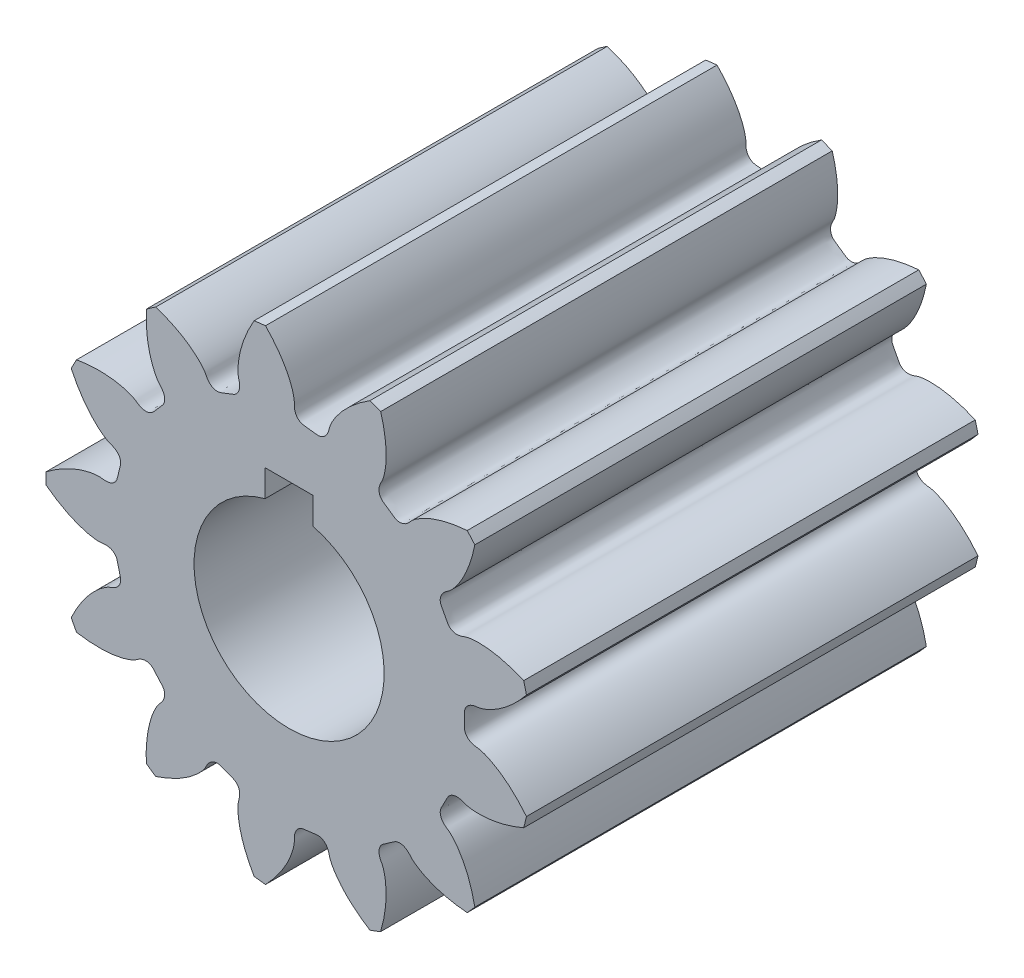
SolidWorks part; units mm, degrees
material "AISI 4130 Steel, annealed at 865C"
ref_plane "Front Plane" through (0, 0, 0) normal (0, 0, 1) x (1, 0, 0)
ref_plane "Top Plane" through (0, 0, 0) normal (0, 1, 0) x (1, 0, 0)
ref_plane "Right Plane" through (0, 0, 0) normal (1, 0, 0) x (0, 0, -1)
ref_plane "Plane1" through (0, 0, 9.5) normal (0, 0, 1) x (1, 0, 0)
sketch "Sketch1" plane through (0, 0, 9.5) normal (0, 0, 1) x (1, 0, 0)
  line L0 (1.01, 5) -> (1.01, 3.8704)
  line L1 (-1.01, 3.8704) -> (-1.01, 5)
  line L2 (-1.01, 5) -> (1.01, 5)
  arc A0 (1.01, 3.8704) -> (-1.01, 3.8704) centre (0, 0) cw
  arc A1 (7.8147, 6.6005) -> (7.4944, 6.9621) centre (0, 0) ccw
  arc A2 (3.8522, 9.4762) -> (3.4005, 9.6475) centre (0, 0) ccw
  arc A3 (-0.9929, 10.1809) -> (-1.4725, 10.1227) centre (0, 0) ccw
  arc A4 (-5.6104, 8.5534) -> (-6.008, 8.2789) centre (0, 0) ccw
  arc A5 (-8.9427, 4.9663) -> (-9.1673, 4.5385) centre (0, 0) ccw
  arc A6 (-10.2264, 0.2416) -> (-10.2264, -0.2416) centre (0, 0) ccw
  arc A7 (-9.1673, -4.5385) -> (-8.9427, -4.9663) centre (0, 0) ccw
  arc A8 (-6.008, -8.2789) -> (-5.6104, -8.5534) centre (0, 0) ccw
  arc A9 (-1.4725, -10.1227) -> (-0.9929, -10.1809) centre (0, 0) ccw
  arc A10 (3.4005, -9.6475) -> (3.8522, -9.4762) centre (0, 0) ccw
  arc A11 (7.4944, -6.9621) -> (7.8147, -6.6005) centre (0, 0) ccw
  arc A12 (9.8714, -2.6819) -> (9.987, -2.2128) centre (0, 0) ccw
  arc A13 (9.987, 2.2128) -> (9.8714, 2.6819) centre (0, 0) ccw
  spline S0 degree 3 poles (3.8522, 9.4762) (3.9191, 9.2499) (3.99, 8.9516) (4.0451, 8.5838) (4.0666, 8.3872) (4.0793, 8.2028) (4.0843, 8.0307) (4.0826, 7.8712) (4.0751, 7.7248) (4.063, 7.5914) (4.0473, 7.4713) (4.0289, 7.3644) (4.009, 7.2709) (3.9885, 7.1905) (3.9684, 7.1233) (3.9499, 7.069) (3.9338, 7.0274) (3.9101, 6.9717) (3.8779, 6.9207) (3.8503, 6.8634) (3.8331, 6.8241) (3.818, 6.7841) (3.805, 6.7428) (3.7942, 6.6993) (3.7861, 6.652) (3.7819, 6.5989) (3.7839, 6.5372) (3.7968, 6.4642) (3.8286, 6.3799) (3.8867, 6.2926) (4.0132, 6.1898) (4.199, 6.0833) (4.3645, 5.9473) (4.5054, 5.8655) (4.6076, 5.8421) (4.6978, 5.8423) (4.7706, 5.8562) (4.829, 5.8761) (4.8771, 5.8989) (4.9185, 5.9232) (4.9554, 5.9487) (4.9894, 5.9756) (5.0214, 6.0039) (5.052, 6.0339) (5.0959, 6.0801) (5.1321, 6.1282) (5.1758, 6.1701) (5.209, 6.1999) (5.2532, 6.2365) (5.3089, 6.2791) (5.3768, 6.3267) (5.4572, 6.3785) (5.5506, 6.4336) (5.6573, 6.4909) (5.7777, 6.5496) (5.912, 6.6084) (6.0605, 6.6666) (6.2232, 6.7229) (6.4002, 6.7765) (6.5916, 6.8261) (6.955, 6.905) (7.2591, 6.9445) (7.4944, 6.9621) knots 0 0 0 0 0.096899 0.125711 0.152776 0.178096 0.201669 0.223496 0.243577 0.261912 0.2785 0.293343 0.306439 0.317789 0.327393 0.335251 0.341362 0.345728 0.360077 0.366027 0.371876 0.377693 0.383571 0.389648 0.396117 0.403265 0.411505 0.421399 0.433571 0.448325 0.46384 0.5 0.53616 0.551675 0.566429 0.578601 0.588495 0.596735 0.603883 0.610352 0.616429 0.622307 0.628124 0.633973 0.639923 0.654272 0.658638 0.664749 0.672607 0.682211 0.693561 0.706657 0.7215 0.738088 0.756423 0.776504 0.798331 0.821904 0.847224 0.874289 0.903101 1 1 1 1
  spline S1 degree 3 poles (-0.9929, 10.1809) (-0.8284, 10.0117) (-0.6271, 9.7805) (-0.4073, 9.4804) (-0.297, 9.3164) (-0.2, 9.1589) (-0.1156, 9.0089) (-0.043, 8.8669) (0.0185, 8.7337) (0.0697, 8.61) (0.1116, 8.4963) (0.145, 8.3932) (0.1708, 8.3011) (0.19, 8.2204) (0.2035, 8.1516) (0.2124, 8.0949) (0.2174, 8.0506) (0.2223, 7.9903) (0.2175, 7.9302) (0.2197, 7.8665) (0.2228, 7.8238) (0.228, 7.7813) (0.2356, 7.7387) (0.2462, 7.6951) (0.2611, 7.6495) (0.2821, 7.6005) (0.3125, 7.5469) (0.3578, 7.4883) (0.4252, 7.4283) (0.5172, 7.3781) (0.6769, 7.3459) (0.891, 7.3379) (1.1007, 7.2944) (1.2635, 7.2875) (1.3649, 7.3142) (1.4446, 7.3563) (1.5027, 7.4024) (1.5451, 7.4472) (1.5771, 7.4897) (1.6025, 7.5305) (1.6233, 7.5702) (1.6409, 7.6098) (1.6561, 7.6497) (1.6693, 7.6905) (1.6866, 7.7518) (1.6963, 7.8113) (1.7155, 7.8686) (1.731, 7.9105) (1.7532, 7.9634) (1.7828, 8.027) (1.8207, 8.1007) (1.8678, 8.184) (1.9249, 8.2761) (1.9928, 8.3765) (2.0722, 8.4844) (2.1638, 8.5989) (2.2682, 8.7194) (2.386, 8.8449) (2.5179, 8.9746) (2.6643, 9.1074) (2.9495, 9.3462) (3.2003, 9.5225) (3.4005, 9.6475) knots 0 0 0 0 0.096899 0.125711 0.152776 0.178096 0.201669 0.223496 0.243577 0.261912 0.2785 0.293343 0.306439 0.317789 0.327393 0.335251 0.341362 0.345728 0.360077 0.366027 0.371876 0.377693 0.383571 0.389648 0.396117 0.403265 0.411505 0.421399 0.433571 0.448325 0.46384 0.5 0.53616 0.551675 0.566429 0.578601 0.588495 0.596735 0.603883 0.610352 0.616429 0.622307 0.628124 0.633973 0.639923 0.654272 0.658638 0.664749 0.672607 0.682211 0.693561 0.706657 0.7215 0.738088 0.756423 0.776504 0.798331 0.821904 0.847224 0.874289 0.903101 1 1 1 1
  spline S2 degree 3 poles (-5.6104, 8.5534) (-5.3862, 8.4799) (-5.1005, 8.3688) (-4.7664, 8.2052) (-4.5925, 8.1112) (-4.4334, 8.0169) (-4.289, 7.9232) (-4.1587, 7.8313) (-4.0424, 7.7419) (-3.9395, 7.6562) (-3.8496, 7.575) (-3.7721, 7.4992) (-3.7065, 7.4296) (-3.652, 7.3671) (-3.608, 7.3125) (-3.5738, 7.2664) (-3.5488, 7.2294) (-3.5164, 7.1784) (-3.4927, 7.1229) (-3.4612, 7.0676) (-3.4386, 7.0311) (-3.4143, 6.996) (-3.3878, 6.9618) (-3.3581, 6.9282) (-3.3237, 6.8947) (-3.2824, 6.861) (-3.2305, 6.8277) (-3.1631, 6.7968) (-3.0756, 6.775) (-2.9708, 6.7733) (-2.8144, 6.819) (-2.6212, 6.9114) (-2.4153, 6.9704) (-2.2679, 7.0399) (-2.1905, 7.1107) (-2.1395, 7.185) (-2.1095, 7.2528) (-2.0928, 7.3122) (-2.0842, 7.3648) (-2.0807, 7.4126) (-2.0807, 7.4575) (-2.0835, 7.5007) (-2.0886, 7.5431) (-2.0959, 7.5854) (-2.109, 7.6477) (-2.1281, 7.7049) (-2.1377, 7.7646) (-2.1434, 7.8088) (-2.1484, 7.866) (-2.1518, 7.9361) (-2.1524, 8.019) (-2.1494, 8.1146) (-2.1417, 8.2227) (-2.1282, 8.3431) (-2.1081, 8.4755) (-2.0802, 8.6195) (-2.0438, 8.7747) (-1.9977, 8.9406) (-1.9412, 9.1167) (-1.8733, 9.3024) (-1.7318, 9.6464) (-1.5916, 9.9191) (-1.4725, 10.1227) knots 0 0 0 0 0.096899 0.125711 0.152776 0.178096 0.201669 0.223496 0.243577 0.261912 0.2785 0.293343 0.306439 0.317789 0.327393 0.335251 0.341362 0.345728 0.360077 0.366027 0.371876 0.377693 0.383571 0.389648 0.396117 0.403265 0.411505 0.421399 0.433571 0.448325 0.46384 0.5 0.53616 0.551675 0.566429 0.578601 0.588495 0.596735 0.603883 0.610352 0.616429 0.622307 0.628124 0.633973 0.639923 0.654272 0.658638 0.664749 0.672607 0.682211 0.693561 0.706657 0.7215 0.738088 0.756423 0.776504 0.798331 0.821904 0.847224 0.874289 0.903101 1 1 1 1
  spline S3 degree 3 poles (-8.9427, 4.9663) (-8.7101, 5.0055) (-8.4054, 5.0399) (-8.0336, 5.0502) (-7.8359, 5.0479) (-7.6512, 5.0383) (-7.4798, 5.0225) (-7.3217, 5.0016) (-7.1772, 4.9765) (-7.0463, 4.9484) (-6.9289, 4.9183) (-6.8251, 4.8872) (-6.7346, 4.8561) (-6.6574, 4.8261) (-6.593, 4.7981) (-6.5413, 4.7732) (-6.502, 4.7522) (-6.4496, 4.722) (-6.4028, 4.6839) (-6.3492, 4.6495) (-6.3123, 4.6277) (-6.2744, 4.6079) (-6.235, 4.59) (-6.1931, 4.574) (-6.1471, 4.5603) (-6.0949, 4.5497) (-6.0334, 4.5443) (-5.9594, 4.5483) (-5.8718, 4.5697) (-5.7782, 4.6169) (-5.661, 4.73) (-5.5328, 4.9017) (-5.3779, 5.0495) (-5.2797, 5.1796) (-5.2441, 5.2782) (-5.2335, 5.3678) (-5.2384, 5.4417) (-5.2512, 5.502) (-5.268, 5.5526) (-5.2871, 5.5966) (-5.3081, 5.6363) (-5.3306, 5.6733) (-5.3548, 5.7085) (-5.3809, 5.7425) (-5.4215, 5.7916) (-5.465, 5.8334) (-5.5012, 5.8818) (-5.5269, 5.9183) (-5.5578, 5.9666) (-5.5934, 6.0271) (-5.6325, 6.1002) (-5.6742, 6.1862) (-5.7176, 6.2856) (-5.7617, 6.3985) (-5.8054, 6.525) (-5.8476, 6.6655) (-5.8875, 6.8199) (-5.9238, 6.9882) (-5.9556, 7.1703) (-5.9818, 7.3663) (-6.0163, 7.7366) (-6.0189, 8.0432) (-6.008, 8.2789) knots 0 0 0 0 0.096899 0.125711 0.152776 0.178096 0.201669 0.223496 0.243577 0.261912 0.2785 0.293343 0.306439 0.317789 0.327393 0.335251 0.341362 0.345728 0.360077 0.366027 0.371876 0.377693 0.383571 0.389648 0.396117 0.403265 0.411505 0.421399 0.433571 0.448325 0.46384 0.5 0.53616 0.551675 0.566429 0.578601 0.588495 0.596735 0.603883 0.610352 0.616429 0.622307 0.628124 0.633973 0.639923 0.654272 0.658638 0.664749 0.672607 0.682211 0.693561 0.706657 0.7215 0.738088 0.756423 0.776504 0.798331 0.821904 0.847224 0.874289 0.903101 1 1 1 1
  spline S4 degree 3 poles (-10.2264, 0.2416) (-10.0386, 0.3844) (-9.7848, 0.5564) (-9.4604, 0.7384) (-9.2842, 0.8281) (-9.1162, 0.9055) (-8.9571, 0.9712) (-8.8074, 1.0261) (-8.6678, 1.0711) (-8.5388, 1.107) (-8.4209, 1.1349) (-8.3145, 1.1556) (-8.22, 1.1702) (-8.1376, 1.1795) (-8.0676, 1.1846) (-8.0103, 1.1865) (-7.9656, 1.1862) (-7.9052, 1.1838) (-7.8461, 1.1718) (-7.7827, 1.1663) (-7.7399, 1.1642) (-7.6971, 1.1642) (-7.6539, 1.1666) (-7.6094, 1.172) (-7.5623, 1.1812) (-7.5111, 1.1962) (-7.4542, 1.2199) (-7.3905, 1.2578) (-7.3229, 1.3175) (-7.262, 1.4028) (-7.2107, 1.5575) (-7.177, 1.769) (-7.1085, 1.9719) (-7.082, 2.1327) (-7.0964, 2.2366) (-7.1285, 2.3208) (-7.1673, 2.384) (-7.2066, 2.4314) (-7.245, 2.4684) (-7.2824, 2.4985) (-7.3194, 2.5239) (-7.3565, 2.5462) (-7.3943, 2.5661) (-7.4332, 2.5841) (-7.492, 2.6087) (-7.5499, 2.6255) (-7.6045, 2.6515) (-7.6442, 2.6719) (-7.694, 2.7003) (-7.7536, 2.7373) (-7.8222, 2.7839) (-7.8992, 2.8407) (-7.9838, 2.9085) (-8.0752, 2.988) (-8.1727, 3.0797) (-8.2754, 3.1845) (-8.3824, 3.3026) (-8.4928, 3.4348) (-8.6056, 3.5813) (-8.7199, 3.7427) (-8.9225, 4.0546) (-9.0673, 4.3248) (-9.1673, 4.5385) knots 0 0 0 0 0.096899 0.125711 0.152776 0.178096 0.201669 0.223496 0.243577 0.261912 0.2785 0.293343 0.306439 0.317789 0.327393 0.335251 0.341362 0.345728 0.360077 0.366027 0.371876 0.377693 0.383571 0.389648 0.396117 0.403265 0.411505 0.421399 0.433571 0.448325 0.46384 0.5 0.53616 0.551675 0.566429 0.578601 0.588495 0.596735 0.603883 0.610352 0.616429 0.622307 0.628124 0.633973 0.639923 0.654272 0.658638 0.664749 0.672607 0.682211 0.693561 0.706657 0.7215 0.738088 0.756423 0.776504 0.798331 0.821904 0.847224 0.874289 0.903101 1 1 1 1
  spline S5 degree 3 poles (-9.1673, -4.5385) (-9.0673, -4.3248) (-8.9225, -4.0546) (-8.7199, -3.7427) (-8.6056, -3.5813) (-8.4928, -3.4348) (-8.3824, -3.3026) (-8.2754, -3.1845) (-8.1727, -3.0797) (-8.0752, -2.988) (-7.9838, -2.9085) (-7.8992, -2.8407) (-7.8222, -2.7839) (-7.7536, -2.7373) (-7.694, -2.7003) (-7.6442, -2.6719) (-7.6045, -2.6515) (-7.5499, -2.6255) (-7.492, -2.6087) (-7.4332, -2.5841) (-7.3943, -2.5661) (-7.3565, -2.5462) (-7.3194, -2.5239) (-7.2824, -2.4985) (-7.245, -2.4684) (-7.2066, -2.4314) (-7.1673, -2.384) (-7.1285, -2.3208) (-7.0964, -2.2366) (-7.082, -2.1327) (-7.1085, -1.9719) (-7.177, -1.769) (-7.2107, -1.5575) (-7.262, -1.4028) (-7.3229, -1.3175) (-7.3905, -1.2578) (-7.4542, -1.2199) (-7.5111, -1.1962) (-7.5623, -1.1812) (-7.6094, -1.172) (-7.6539, -1.1666) (-7.6971, -1.1642) (-7.7399, -1.1642) (-7.7827, -1.1663) (-7.8461, -1.1718) (-7.9052, -1.1838) (-7.9656, -1.1862) (-8.0103, -1.1865) (-8.0676, -1.1846) (-8.1376, -1.1795) (-8.22, -1.1702) (-8.3145, -1.1556) (-8.4209, -1.1349) (-8.5388, -1.107) (-8.6678, -1.0711) (-8.8074, -1.0261) (-8.9571, -0.9712) (-9.1162, -0.9055) (-9.2842, -0.8281) (-9.4604, -0.7384) (-9.7848, -0.5564) (-10.0386, -0.3844) (-10.2264, -0.2416) knots 0 0 0 0 0.096899 0.125711 0.152776 0.178096 0.201669 0.223496 0.243577 0.261912 0.2785 0.293343 0.306439 0.317789 0.327393 0.335251 0.341362 0.345728 0.360077 0.366027 0.371876 0.377693 0.383571 0.389648 0.396117 0.403265 0.411505 0.421399 0.433571 0.448325 0.46384 0.5 0.53616 0.551675 0.566429 0.578601 0.588495 0.596735 0.603883 0.610352 0.616429 0.622307 0.628124 0.633973 0.639923 0.654272 0.658638 0.664749 0.672607 0.682211 0.693561 0.706657 0.7215 0.738088 0.756423 0.776504 0.798331 0.821904 0.847224 0.874289 0.903101 1 1 1 1
  spline S6 degree 3 poles (-6.008, -8.2789) (-6.0189, -8.0432) (-6.0163, -7.7366) (-5.9818, -7.3663) (-5.9556, -7.1703) (-5.9238, -6.9882) (-5.8875, -6.8199) (-5.8476, -6.6655) (-5.8054, -6.525) (-5.7617, -6.3985) (-5.7176, -6.2856) (-5.6742, -6.1862) (-5.6325, -6.1002) (-5.5934, -6.0271) (-5.5578, -5.9666) (-5.5269, -5.9183) (-5.5012, -5.8818) (-5.465, -5.8334) (-5.4215, -5.7916) (-5.3809, -5.7425) (-5.3548, -5.7084) (-5.3306, -5.6733) (-5.3081, -5.6363) (-5.2871, -5.5966) (-5.268, -5.5526) (-5.2512, -5.502) (-5.2384, -5.4417) (-5.2335, -5.3678) (-5.2441, -5.2782) (-5.2797, -5.1796) (-5.3779, -5.0495) (-5.5328, -4.9017) (-5.661, -4.73) (-5.7782, -4.6169) (-5.8718, -4.5697) (-5.9594, -4.5483) (-6.0334, -4.5443) (-6.0949, -4.5497) (-6.1471, -4.5603) (-6.1931, -4.574) (-6.235, -4.59) (-6.2744, -4.6079) (-6.3123, -4.6277) (-6.3492, -4.6495) (-6.4028, -4.6839) (-6.4496, -4.722) (-6.502, -4.7522) (-6.5413, -4.7732) (-6.593, -4.7981) (-6.6574, -4.8261) (-6.7346, -4.8561) (-6.8251, -4.8872) (-6.9289, -4.9183) (-7.0463, -4.9484) (-7.1772, -4.9765) (-7.3217, -5.0016) (-7.4798, -5.0225) (-7.6512, -5.0383) (-7.8359, -5.0479) (-8.0336, -5.0502) (-8.4054, -5.0399) (-8.7101, -5.0055) (-8.9427, -4.9663) knots 0 0 0 0 0.096899 0.125711 0.152776 0.178096 0.201669 0.223496 0.243577 0.261912 0.2785 0.293343 0.306439 0.317789 0.327393 0.335251 0.341362 0.345728 0.360077 0.366027 0.371876 0.377693 0.383571 0.389648 0.396117 0.403265 0.411505 0.421399 0.433571 0.448325 0.46384 0.5 0.53616 0.551675 0.566429 0.578601 0.588495 0.596735 0.603883 0.610352 0.616429 0.622307 0.628124 0.633973 0.639923 0.654272 0.658638 0.664749 0.672607 0.682211 0.693561 0.706657 0.7215 0.738088 0.756423 0.776504 0.798331 0.821904 0.847224 0.874289 0.903101 1 1 1 1
  spline S7 degree 3 poles (-1.4725, -10.1227) (-1.5916, -9.9191) (-1.7318, -9.6464) (-1.8733, -9.3024) (-1.9412, -9.1167) (-1.9977, -8.9406) (-2.0438, -8.7747) (-2.0802, -8.6195) (-2.1081, -8.4755) (-2.1282, -8.3431) (-2.1417, -8.2227) (-2.1494, -8.1146) (-2.1524, -8.019) (-2.1518, -7.9361) (-2.1484, -7.866) (-2.1434, -7.8088) (-2.1377, -7.7646) (-2.1281, -7.7049) (-2.109, -7.6477) (-2.0959, -7.5854) (-2.0886, -7.5431) (-2.0835, -7.5007) (-2.0807, -7.4575) (-2.0807, -7.4126) (-2.0842, -7.3648) (-2.0928, -7.3122) (-2.1095, -7.2528) (-2.1395, -7.185) (-2.1905, -7.1107) (-2.2679, -7.0399) (-2.4153, -6.9704) (-2.6212, -6.9114) (-2.8144, -6.819) (-2.9708, -6.7733) (-3.0756, -6.775) (-3.1631, -6.7968) (-3.2305, -6.8277) (-3.2824, -6.861) (-3.3237, -6.8947) (-3.3581, -6.9282) (-3.3878, -6.9618) (-3.4143, -6.996) (-3.4386, -7.0311) (-3.4612, -7.0676) (-3.4927, -7.1229) (-3.5164, -7.1784) (-3.5488, -7.2294) (-3.5738, -7.2664) (-3.608, -7.3125) (-3.652, -7.3671) (-3.7065, -7.4296) (-3.7721, -7.4992) (-3.8496, -7.575) (-3.9395, -7.6562) (-4.0424, -7.7419) (-4.1587, -7.8313) (-4.289, -7.9232) (-4.4334, -8.0169) (-4.5925, -8.1112) (-4.7664, -8.2052) (-5.1005, -8.3688) (-5.3862, -8.4799) (-5.6104, -8.5534) knots 0 0 0 0 0.096899 0.125711 0.152776 0.178096 0.201669 0.223496 0.243577 0.261912 0.2785 0.293343 0.306439 0.317789 0.327393 0.335251 0.341362 0.345728 0.360077 0.366027 0.371876 0.377693 0.383571 0.389648 0.396117 0.403265 0.411505 0.421399 0.433571 0.448325 0.46384 0.5 0.53616 0.551675 0.566429 0.578601 0.588495 0.596735 0.603883 0.610352 0.616429 0.622307 0.628124 0.633973 0.639923 0.654272 0.658638 0.664749 0.672607 0.682211 0.693561 0.706657 0.7215 0.738088 0.756423 0.776504 0.798331 0.821904 0.847224 0.874289 0.903101 1 1 1 1
  spline S8 degree 3 poles (3.4005, -9.6475) (3.2003, -9.5225) (2.9495, -9.3462) (2.6643, -9.1074) (2.5179, -8.9746) (2.386, -8.8449) (2.2682, -8.7194) (2.1638, -8.5989) (2.0722, -8.4844) (1.9928, -8.3765) (1.9249, -8.2761) (1.8678, -8.184) (1.8207, -8.1007) (1.7828, -8.027) (1.7532, -7.9634) (1.731, -7.9105) (1.7155, -7.8686) (1.6963, -7.8113) (1.6866, -7.7518) (1.6693, -7.6905) (1.6561, -7.6497) (1.6409, -7.6098) (1.6233, -7.5702) (1.6025, -7.5305) (1.5771, -7.4897) (1.5451, -7.4472) (1.5027, -7.4024) (1.4446, -7.3563) (1.3649, -7.3142) (1.2635, -7.2875) (1.1007, -7.2944) (0.891, -7.3379) (0.6769, -7.3459) (0.5172, -7.3781) (0.4252, -7.4283) (0.3578, -7.4883) (0.3125, -7.5469) (0.2821, -7.6005) (0.2611, -7.6495) (0.2462, -7.6952) (0.2356, -7.7387) (0.228, -7.7813) (0.2228, -7.8238) (0.2197, -7.8665) (0.2175, -7.9302) (0.2223, -7.9903) (0.2174, -8.0506) (0.2124, -8.0949) (0.2035, -8.1516) (0.19, -8.2204) (0.1708, -8.3011) (0.145, -8.3932) (0.1116, -8.4963) (0.0697, -8.61) (0.0185, -8.7337) (-0.043, -8.8669) (-0.1156, -9.0089) (-0.2, -9.1589) (-0.297, -9.3164) (-0.4073, -9.4804) (-0.6271, -9.7805) (-0.8284, -10.0117) (-0.9929, -10.1809) knots 0 0 0 0 0.096899 0.125711 0.152776 0.178096 0.201669 0.223496 0.243577 0.261912 0.2785 0.293343 0.306439 0.317789 0.327393 0.335251 0.341362 0.345728 0.360077 0.366027 0.371876 0.377693 0.383571 0.389648 0.396117 0.403265 0.411505 0.421399 0.433571 0.448325 0.46384 0.5 0.53616 0.551675 0.566429 0.578601 0.588495 0.596735 0.603883 0.610352 0.616429 0.622307 0.628124 0.633973 0.639923 0.654272 0.658638 0.664749 0.672607 0.682211 0.693561 0.706657 0.7215 0.738088 0.756423 0.776504 0.798331 0.821904 0.847224 0.874289 0.903101 1 1 1 1
  spline S9 degree 3 poles (7.4944, -6.9621) (7.2591, -6.9445) (6.955, -6.905) (6.5916, -6.8261) (6.4002, -6.7765) (6.2232, -6.7229) (6.0605, -6.6666) (5.912, -6.6084) (5.7777, -6.5496) (5.6573, -6.4909) (5.5506, -6.4336) (5.4572, -6.3785) (5.3768, -6.3267) (5.3089, -6.2791) (5.2532, -6.2365) (5.209, -6.1999) (5.1758, -6.1701) (5.1321, -6.1282) (5.0959, -6.0801) (5.052, -6.0339) (5.0214, -6.0039) (4.9894, -5.9756) (4.9554, -5.9487) (4.9185, -5.9232) (4.8771, -5.8989) (4.829, -5.8761) (4.7706, -5.8562) (4.6978, -5.8423) (4.6076, -5.8421) (4.5054, -5.8655) (4.3645, -5.9473) (4.199, -6.0833) (4.0132, -6.1898) (3.8867, -6.2926) (3.8286, -6.3799) (3.7968, -6.4642) (3.7839, -6.5372) (3.7819, -6.5989) (3.7861, -6.652) (3.7942, -6.6993) (3.805, -6.7428) (3.818, -6.7841) (3.8331, -6.8241) (3.8503, -6.8634) (3.8779, -6.9207) (3.9101, -6.9717) (3.9338, -7.0274) (3.9499, -7.069) (3.9684, -7.1233) (3.9885, -7.1905) (4.009, -7.2709) (4.0289, -7.3644) (4.0473, -7.4713) (4.063, -7.5914) (4.0751, -7.7248) (4.0826, -7.8712) (4.0843, -8.0307) (4.0793, -8.2028) (4.0666, -8.3872) (4.0451, -8.5838) (3.99, -8.9516) (3.9191, -9.2499) (3.8522, -9.4762) knots 0 0 0 0 0.096899 0.125711 0.152776 0.178096 0.201669 0.223496 0.243577 0.261912 0.2785 0.293343 0.306439 0.317789 0.327393 0.335251 0.341362 0.345728 0.360077 0.366027 0.371876 0.377693 0.383571 0.389648 0.396117 0.403265 0.411505 0.421399 0.433571 0.448325 0.46384 0.5 0.53616 0.551675 0.566429 0.578601 0.588495 0.596735 0.603883 0.610352 0.616429 0.622307 0.628124 0.633973 0.639923 0.654272 0.658638 0.664749 0.672607 0.682211 0.693561 0.706657 0.7215 0.738088 0.756423 0.776504 0.798331 0.821904 0.847224 0.874289 0.903101 1 1 1 1
  spline S10 degree 3 poles (9.8714, -2.6819) (9.6549, -2.7756) (9.3673, -2.8819) (9.0088, -2.9809) (8.8163, -3.0259) (8.6347, -3.0608) (8.4644, -3.0865) (8.3059, -3.104) (8.1596, -3.1143) (8.0258, -3.1184) (7.9046, -3.1172) (7.7964, -3.1118) (7.7011, -3.1033) (7.6189, -3.0927) (7.5497, -3.0809) (7.4936, -3.069) (7.4503, -3.058) (7.3922, -3.0413) (7.3377, -3.0155) (7.2774, -2.9949) (7.2363, -2.9826) (7.1949, -2.9724) (7.1523, -2.9644) (7.1078, -2.959) (7.0598, -2.9567) (7.0066, -2.9589) (6.9456, -2.9684) (6.8748, -2.99) (6.7948, -3.0317) (6.7152, -3.0999) (6.6284, -3.2378) (6.5451, -3.4351) (6.4301, -3.6158) (6.3659, -3.7656) (6.3549, -3.8698) (6.366, -3.9593) (6.3885, -4.0299) (6.4154, -4.0855) (6.4438, -4.1305) (6.4729, -4.1687) (6.5027, -4.2022) (6.5334, -4.2327) (6.5654, -4.2611) (6.5988, -4.2879) (6.65, -4.3258) (6.7022, -4.356) (6.749, -4.3943) (6.7826, -4.4237) (6.8242, -4.4632) (6.8732, -4.5134) (6.9287, -4.575) (6.9898, -4.6485) (7.0557, -4.7346) (7.1255, -4.8337) (7.1982, -4.9461) (7.2729, -5.0724) (7.3485, -5.2127) (7.424, -5.3674) (7.4985, -5.5367) (7.5708, -5.7207) (7.693, -6.072) (7.7689, -6.3691) (7.8147, -6.6005) knots 0 0 0 0 0.096899 0.125711 0.152776 0.178096 0.201669 0.223496 0.243577 0.261912 0.2785 0.293343 0.306439 0.317789 0.327393 0.335251 0.341362 0.345728 0.360077 0.366027 0.371876 0.377693 0.383571 0.389648 0.396117 0.403265 0.411505 0.421399 0.433571 0.448325 0.46384 0.5 0.53616 0.551675 0.566429 0.578601 0.588495 0.596735 0.603883 0.610352 0.616429 0.622307 0.628124 0.633973 0.639923 0.654272 0.658638 0.664749 0.672607 0.682211 0.693561 0.706657 0.7215 0.738088 0.756423 0.776504 0.798331 0.821904 0.847224 0.874289 0.903101 1 1 1 1
  spline S11 degree 3 poles (9.987, 2.2128) (9.8389, 2.0292) (9.6336, 1.8014) (9.3622, 1.5471) (9.2126, 1.4178) (9.068, 1.3025) (8.9292, 1.2006) (8.7971, 1.1115) (8.6723, 1.0344) (8.5556, 0.9686) (8.4478, 0.9133) (8.3495, 0.8677) (8.2611, 0.831) (8.1834, 0.8022) (8.1167, 0.7805) (8.0615, 0.7649) (8.0181, 0.7546) (7.9588, 0.7424) (7.8986, 0.7399) (7.8357, 0.7301) (7.7936, 0.7219) (7.7521, 0.7116) (7.7107, 0.699) (7.6687, 0.6831) (7.6252, 0.6629) (7.5791, 0.6361) (7.5295, 0.5994) (7.4768, 0.5474) (7.4254, 0.4733) (7.3866, 0.3759) (7.3739, 0.2134) (7.3918, 0) (7.3739, -0.2134) (7.3866, -0.3759) (7.4254, -0.4733) (7.4768, -0.5474) (7.5295, -0.5994) (7.5791, -0.6361) (7.6252, -0.6629) (7.6687, -0.6831) (7.7107, -0.699) (7.7521, -0.7116) (7.7936, -0.7219) (7.8357, -0.7301) (7.8986, -0.7399) (7.9588, -0.7424) (8.0181, -0.7546) (8.0615, -0.7649) (8.1167, -0.7805) (8.1834, -0.8022) (8.2611, -0.831) (8.3495, -0.8677) (8.4478, -0.9133) (8.5556, -0.9686) (8.6723, -1.0344) (8.7971, -1.1115) (8.9292, -1.2006) (9.068, -1.3025) (9.2126, -1.4178) (9.3622, -1.5471) (9.6336, -1.8014) (9.8389, -2.0292) (9.987, -2.2128) knots 0 0 0 0 0.096899 0.125711 0.152776 0.178096 0.201669 0.223496 0.243577 0.261912 0.2785 0.293343 0.306439 0.317789 0.327393 0.335251 0.341362 0.345728 0.360077 0.366027 0.371876 0.377693 0.383571 0.389648 0.396117 0.403265 0.411505 0.421399 0.433571 0.448325 0.46384 0.5 0.53616 0.551675 0.566429 0.578601 0.588495 0.596735 0.603883 0.610352 0.616429 0.622307 0.628124 0.633973 0.639923 0.654272 0.658638 0.664749 0.672607 0.682211 0.693561 0.706657 0.7215 0.738088 0.756423 0.776504 0.798331 0.821904 0.847224 0.874289 0.903101 1 1 1 1
  spline S12 degree 3 poles (7.8147, 6.6005) (7.7689, 6.3691) (7.693, 6.072) (7.5708, 5.7207) (7.4985, 5.5367) (7.424, 5.3674) (7.3485, 5.2127) (7.2729, 5.0724) (7.1982, 4.9461) (7.1255, 4.8337) (7.0557, 4.7346) (6.9898, 4.6485) (6.9287, 4.575) (6.8732, 4.5134) (6.8242, 4.4632) (6.7826, 4.4237) (6.749, 4.3943) (6.7022, 4.356) (6.65, 4.3258) (6.5988, 4.2879) (6.5654, 4.2611) (6.5334, 4.2327) (6.5027, 4.2022) (6.4729, 4.1687) (6.4438, 4.1305) (6.4154, 4.0855) (6.3885, 4.0299) (6.366, 3.9593) (6.3549, 3.8698) (6.3659, 3.7656) (6.4301, 3.6158) (6.5451, 3.4351) (6.6284, 3.2378) (6.7152, 3.0999) (6.7948, 3.0317) (6.8748, 2.99) (6.9456, 2.9684) (7.0066, 2.9589) (7.0598, 2.9567) (7.1078, 2.959) (7.1523, 2.9644) (7.1949, 2.9724) (7.2363, 2.9826) (7.2774, 2.9949) (7.3377, 3.0155) (7.3922, 3.0413) (7.4503, 3.058) (7.4936, 3.069) (7.5497, 3.0809) (7.6189, 3.0927) (7.7011, 3.1033) (7.7964, 3.1118) (7.9046, 3.1172) (8.0258, 3.1184) (8.1596, 3.1143) (8.3059, 3.104) (8.4644, 3.0865) (8.6347, 3.0608) (8.8163, 3.0259) (9.0088, 2.9809) (9.3673, 2.8819) (9.6549, 2.7756) (9.8714, 2.6819) knots 0 0 0 0 0.096899 0.125711 0.152776 0.178096 0.201669 0.223496 0.243577 0.261912 0.2785 0.293343 0.306439 0.317789 0.327393 0.335251 0.341362 0.345728 0.360077 0.366027 0.371876 0.377693 0.383571 0.389648 0.396117 0.403265 0.411505 0.421399 0.433571 0.448325 0.46384 0.5 0.53616 0.551675 0.566429 0.578601 0.588495 0.596735 0.603883 0.610352 0.616429 0.622307 0.628124 0.633973 0.639923 0.654272 0.658638 0.664749 0.672607 0.682211 0.693561 0.706657 0.7215 0.738088 0.756423 0.776504 0.798331 0.821904 0.847224 0.874289 0.903101 1 1 1 1
extrude "Boss-Extrude1" add sketch "Sketch1" against normal blind 19
